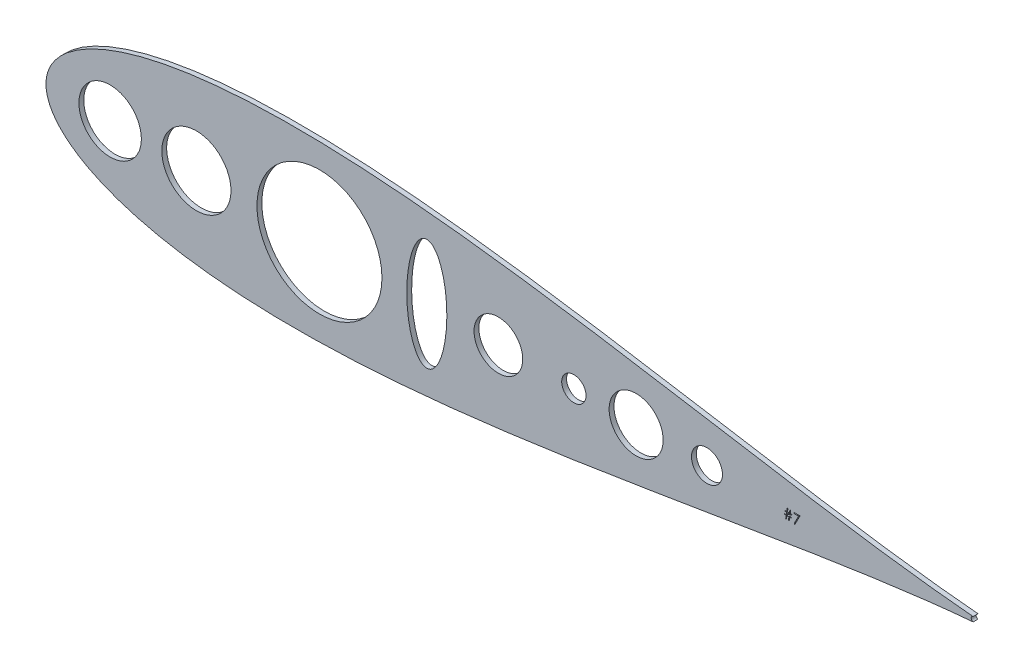
SolidWorks part; units mm, degrees
ref_plane "Front Plane" through (0, 0, 0) normal (0, 0, 1) x (1, 0, 0)
ref_plane "Top Plane" through (0, 0, 0) normal (0, 1, 0) x (1, 0, 0)
ref_plane "Right Plane" through (0, 0, 0) normal (1, 0, 0) x (0, 0, -1)
sketch "Sketch2" plane through (0, 0, 0) normal (0, 0, 1) x (1, 0, 0)
  line L0 (672.2866, 533.3885) -> (672.2866, 533.0629)
  line L1 (672.2866, 533.0629) -> (671.3157, 533.0629)
  line L2 (671.3157, 533.0629) -> (671.0522, 531.3044)
  line L3 (671.0522, 531.3044) -> (670.6584, 531.3044)
  line L4 (670.6584, 531.3044) -> (670.9219, 533.0629)
  line L5 (670.9219, 533.0629) -> (669.8829, 533.0629)
  line L6 (669.8829, 533.0629) -> (669.6194, 531.3044)
  line L7 (669.6194, 531.3044) -> (669.2255, 531.3044)
  line L8 (669.2255, 531.3044) -> (669.4891, 533.0629)
  line L9 (669.4891, 533.0629) -> (668.6394, 533.0629)
  line L10 (668.6394, 533.0629) -> (668.6394, 533.3885)
  line L11 (668.6394, 533.3885) -> (669.5379, 533.3885)
  line L12 (669.5379, 533.3885) -> (669.714, 534.5608)
  line L13 (669.714, 534.5608) -> (668.7696, 534.5608)
  line L14 (668.7696, 534.5608) -> (668.7696, 534.8865)
  line L15 (668.7696, 534.8865) -> (669.7628, 534.8865)
  line L16 (669.7628, 534.8865) -> (670.0071, 536.5147)
  line L17 (670.0071, 536.5147) -> (670.3999, 536.5147)
  line L18 (670.3999, 536.5147) -> (670.1556, 534.8865)
  line L19 (670.1556, 534.8865) -> (671.1957, 534.8865)
  line L20 (671.1957, 534.8865) -> (671.4399, 536.5147)
  line L21 (671.4399, 536.5147) -> (671.8327, 536.5147)
  line L22 (671.8327, 536.5147) -> (671.5885, 534.8865)
  line L23 (671.5885, 534.8865) -> (672.4168, 534.8865)
  line L24 (672.4168, 534.8865) -> (672.4168, 534.5608)
  line L25 (672.4168, 534.5608) -> (671.5396, 534.5608)
  line L26 (671.5396, 534.5608) -> (671.3646, 533.3885)
  line L27 (671.3646, 533.3885) -> (672.2866, 533.3885)
  line L28 (671.1468, 534.5608) -> (670.1068, 534.5608)
  line L29 (670.1068, 534.5608) -> (669.9318, 533.3885)
  line L30 (669.9318, 533.3885) -> (670.9708, 533.3885)
  line L31 (670.9708, 533.3885) -> (671.1468, 534.5608)
  line L32 (673.5891, 536.3844) -> (676.7153, 536.3844)
  line L33 (676.7153, 536.3844) -> (674.045, 531.1741)
  line L34 (674.045, 531.1741) -> (673.6512, 531.3909)
  line L35 (673.6512, 531.3909) -> (675.9439, 535.8634)
  line L36 (675.9439, 535.8634) -> (673.5891, 535.8634)
  line L37 (673.5891, 535.8634) -> (673.5891, 536.3844)
  line L38 (426.1032, 534.8483) -> (591.2438, 534.8483) construction
  circle A0 centre (316.9415, 534.8483) radius 16.2849
  circle A1 centre (628.1831, 534.8483) radius 8.0865
  circle A2 centre (591.2438, 534.8483) radius 14.0957
  circle A3 centre (558.7673, 534.8483) radius 6.35
  circle A4 centre (519.3973, 534.8483) radius 12.7
  circle A5 centre (426.1032, 534.8483) radius 32.5896
  circle A6 centre (361.9173, 534.8483) radius 18.034
  arc A7 (766.9747, 536.0676) -> (766.9717, 533.6287) centre (767.2222, 534.8479) ccw
  ellipse E0 centre (482.0882, 534.8483) end of major axis (482.0882, 505.747) minor radius 10.4447
  spline S0 degree 3 poles (766.9747, 536.0676) (766.6971, 536.0909) (763.8731, 536.3296) (758.2015, 536.8538) (749.6175, 537.7468) (740.1002, 538.8425) (729.6855, 540.1476) (718.4217, 541.6634) (706.3578, 543.3865) (693.5458, 545.308) (680.0403, 547.4141) (665.8978, 549.6862) (651.1768, 552.1008) (635.9373, 554.6299) (620.241, 557.2418) (604.1511, 559.9008) (587.7317, 562.5686) (571.0485, 565.2042) (554.1682, 567.7646) (537.1589, 570.2057) (520.0896, 572.4831) (503.0308, 574.5523) (486.0541, 576.3696) (469.2323, 577.8932) (452.6394, 579.0834) (436.3507, 579.9034) (420.4428, 580.3201) (404.9933, 580.3046) (390.081, 579.8324) (375.7861, 578.885) (362.1901, 577.4487) (349.3761, 575.517) (337.4295, 573.0892) (326.4387, 570.1734) (316.4967, 566.7868) (307.7025, 562.9594) (300.1631, 558.7421) (293.991, 554.2203) (289.2902, 549.5417) (286.1076, 544.9538) (284.3329, 540.8146) (283.6163, 537.4942) (283.4531, 534.8483) (283.6163, 532.2024) (284.3329, 528.882) (286.1076, 524.7428) (289.2902, 520.1548) (293.991, 515.4763) (300.1631, 510.9545) (307.7025, 506.7371) (316.4967, 502.9098) (326.4387, 499.5231) (337.4295, 496.6074) (349.3761, 494.1796) (362.1901, 492.2478) (375.7861, 490.8115) (390.081, 489.8641) (404.9933, 489.392) (420.4428, 489.3765) (436.3507, 489.7932) (452.6394, 490.6132) (469.2323, 491.8033) (486.0541, 493.327) (503.0308, 495.1443) (520.0896, 497.2135) (537.1589, 499.4908) (554.1682, 501.932) (571.0485, 504.4924) (587.7317, 507.1279) (604.1511, 509.7957) (620.241, 512.4548) (635.9373, 515.0666) (651.1768, 517.5958) (665.8978, 520.0103) (680.0403, 522.2824) (693.5458, 524.3886) (706.3578, 526.3101) (718.4217, 528.0332) (729.6855, 529.5489) (740.1002, 530.854) (749.6175, 531.9498) (758.2015, 532.8428) (763.8721, 533.3669) (766.6951, 533.6055) (766.9717, 533.6287) knots 0.020477 0.020477 0.020477 0.020477 0.021271 0.028553 0.036781 0.04592 0.055932 0.066773 0.078397 0.090755 0.103793 0.117456 0.131686 0.146422 0.1616 0.177156 0.193024 0.209135 0.225421 0.241812 0.258238 0.274629 0.290914 0.307025 0.322893 0.338448 0.353626 0.368361 0.38259 0.396253 0.40929 0.421647 0.43327 0.444109 0.454119 0.463255 0.471479 0.478755 0.485052 0.490344 0.49461 0.497833 0.5 0.502167 0.50539 0.509656 0.514948 0.521245 0.528521 0.536745 0.545881 0.555891 0.56673 0.578353 0.59071 0.603747 0.61741 0.631639 0.646374 0.661552 0.677107 0.692975 0.709086 0.725371 0.741762 0.758188 0.774579 0.790865 0.806976 0.822844 0.8384 0.853578 0.868314 0.882544 0.896207 0.909245 0.921603 0.933227 0.944068 0.95408 0.963219 0.971447 0.978729 0.97952 0.97952 0.97952 0.97952
extrude "Boss-Extrude1" add sketch "Sketch2" along normal blind 2.54 contours A7 S0 L36 L37 L32 L33 L34 L35 L26 L27 L0 L1 L2 L3 L4 L5 L6 L7 L8 L9 L10 L11 L12 L13 L14 L15 L16 L17 L18 L19 L20 L21 L22 L23 L24 L25 A0 A1 A2 A3 A4 A5
